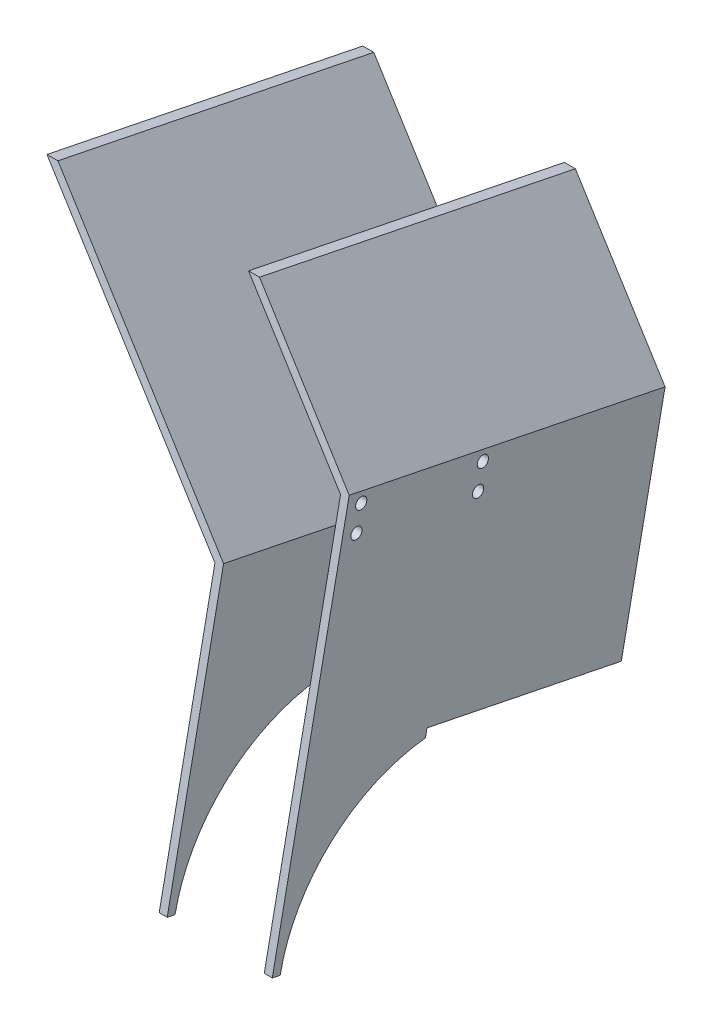
SolidWorks part; units mm, degrees
ref_plane "Front Plane" through (0, 0, 0) normal (0, 0, 1) x (1, 0, 0)
ref_plane "Top Plane" through (0, 0, 0) normal (0, 1, 0) x (1, 0, 0)
ref_plane "Right Plane" through (0, 0, 0) normal (1, 0, 0) x (0, 0, -1)
ref_plane "Plane1" through (0, 77.6466, 383.2116) normal (0, -0.1986, -0.9801) x (0, 0.9801, -0.1986)
sketch "Sketch2" plane through (0, 77.6466, 383.2116) normal (0, -0.1986, -0.9801) x (0, 0.9801, -0.1986)
  line L0 (1912.1833, 36.9944) -> (1826.6109, 116.7919)
  line L1 (1826.6109, 116.7919) -> (1784.1833, 116.7919)
  line L2 (1784.1833, 116.7919) -> (1784.1833, 119.7919)
  line L3 (1784.1833, 119.7919) -> (1827.7926, 119.7919)
  line L4 (1827.7926, 119.7919) -> (1912.1833, 41.0964)
  line L5 (1912.1833, 41.0964) -> (1912.1833, 36.9944)
  point P11 (1832.6072, 119.7919)
  point P15 (0, 0)
extrude "Boss-Extrude1" add sketch "Sketch2" along normal blind 55 and the other way blind 65.5
sketch "Sketch6" plane through (0, 77.6466, 383.2116) normal (0, -0.1986, -0.9801) x (0, 0.9801, -0.1986)
  line L4 (1912.1833, 36.9944) -> (1912.1833, 41.0964) construction
  line L10 (1784.1833, 119.7919) -> (1784.1833, 116.7919) construction
  line L11 (1912.1833, 36.9944) -> (1912.1833, 41.0964) construction
  line L15 (1827.7926, 119.7919) -> (1784.1833, 119.7919) construction
  line L20 (1912.1833, 41.0964) -> (1827.7926, 119.7919) construction
  line L21 (1866.4941, 159.0803) -> (1912.1833, 116.4744)
  line L22 (1865.3124, 156.0803) -> (1912.1833, 112.3725)
  line L23 (1866.4941, 159.0803) -> (1784.1833, 159.0803)
  line L24 (1784.1833, 159.0803) -> (1784.1833, 156.0803)
  line L25 (1784.1833, 156.0803) -> (1865.3124, 156.0803)
  line L26 (1912.1833, 116.4744) -> (1912.1833, 112.3725)
  line L27 (1899.5486, 120.0525) -> (1784.1833, 153.0803) construction
  line L28 (1899.5486, 120.0525) -> (1894.044, 100.8249) construction
  line L29 (1784.1833, 153.0803) -> (1778.6786, 133.8527) construction
  line L30 (1894.044, 100.8249) -> (1778.6786, 133.8527) construction
  line L31 (1909.1833, 71.2405) -> (1821.4208, 153.0803) construction
  line L32 (1909.1833, 71.2405) -> (1895.5433, 56.6134) construction
  line L33 (1821.4208, 153.0803) -> (1807.7809, 138.4532) construction
  line L34 (1895.5433, 56.6134) -> (1807.7809, 138.4532) construction
  point P8 (1894.4598, 112.9489)
  point P10 (1779.949, 153.4132)
  point P14 (1892.6376, 115.3154)
  point P15 (1877.7944, 139.7919)
  point P16 (1741.7419, 149.9509)
  point P17 (1864.3715, 155.4571)
  point P18 (0, 0)
  point P24 (1880.7544, 139.7919)
  point P26 (0, 0)
  point P27 (0, 0)
  point P28 (0, 0)
  point P30 (1876.3324, 132.4324)
  point P32 (0, 0)
  point P33 (1912.1833, 117.8135)
  point P34 (0, 0)
  point P35 (0, 0)
  point P36 (1784.1833, 220.9914)
  point P37 (0, 0)
  point P38 (0, 0)
  point P39 (0, 0)
  point P40 (0, 0)
  point P41 (0, 0)
  point P42 (1784.1833, 173.8319)
  point P43 (1912.1833, 127.5365)
  point P44 (0, 0)
  point P45 (1873.4594, 154.4441)
  point P46 (1797.8232, 175.0854)
  point P50 (1912.1833, 115.9072)
  point P51 (1912.1833, 110.6457)
  point P52 (1912.1833, 114.8107)
  dimension "D1" = 3
  dimension "D2" = 3
  dimension "D3" = 120
  dimension "D4" = 20
  dimension "D5" = 3
  dimension "D6" = 120
  dimension "D7" = 20
  dimension "D8" = 3
  dimension "D9" = 3
  dimension "D10" = 3
extrude "Boss-Extrude3" add sketch "Sketch6" along normal blind 55 and the other way blind 65.5 separate body
sketch "Sketch8" plane through (119.7919, 0, 0) normal (1, 0, 0) x (0, 0, -1)
  line L0 (-93.0945, 1839.3027) -> (-47.6492, 1830.0946)
  line L2 (-93.0945, 1839.3027) -> (25.0055, 1815.3732) construction
  line L3 (-47.6492, 1830.0946) -> (-48.2449, 1827.1543)
  line L4 (-93.0945, 1839.3027) -> (-105.5061, 1778.0475)
  line L5 (-105.5061, 1778.0475) -> (-102.5659, 1777.4518)
  line L7 (-93.0945, 1839.3027) -> (25.0055, 1815.3732) construction
  line L8 (-84.4344, 1882.0435) -> (-93.0945, 1839.3027) construction
  arc A2 (-48.2449, 1827.1543) -> (-102.5659, 1777.4518) centre (-41.3106, 1765.0402) ccw
  point P6 (0, 0)
  dimension "D3" = 62.5
  dimension "D1" = 3
  dimension "D2" = 3
  dimension "D4" = 46.3689
  dimension "D5" = 62.5
extrude "Boss-Extrude5" add sketch "Sketch8" against normal blind 3
sketch "Sketch9" plane through (159.0803, 0, 0) normal (1, 0, 0) x (0, 0, -1)
  line L0 (-93.0945, 1839.3027) -> (-47.6492, 1830.0946)
  line L1 (-47.6492, 1830.0946) -> (-48.2449, 1827.1543)
  line L2 (-93.0945, 1839.3027) -> (-105.5061, 1778.0475)
  line L3 (-105.5061, 1778.0475) -> (-102.5659, 1777.4518)
  line L4 (-93.0945, 1839.3027) -> (25.0055, 1815.3732) construction
  line L6 (-76.7488, 1919.9742) -> (-93.0945, 1839.3027) construction
  arc A0 (-48.2449, 1827.1543) -> (-102.5659, 1777.4518) centre (-41.3106, 1765.0402) ccw
  dimension "D3" = 62.5
  dimension "D1" = 3
  dimension "D2" = 3
  dimension "D4" = 46.3689
  dimension "D5" = 62.5
extrude "Boss-Extrude6" add sketch "Sketch9" against normal blind 3
sketch "Sketch10" plane through (159.0803, 0, 0) normal (1, 0, 0) x (0, 0, -1)
  circle A0 centre (-28.5631, 1897.1397) radius 2.1
  circle A1 centre (-26.7759, 1905.9604) radius 2.1
  circle A2 centre (-72.2504, 1915.1745) radius 2.1
  circle A3 centre (-74.0377, 1906.3537) radius 2.1
  dimension "D1" = 4.2
  dimension "D2" = 4.2
  dimension "D3" = 4.2
  dimension "D4" = 4.2
extrude "Cut-Extrude1" cut sketch "Sketch10" against normal blind 3
